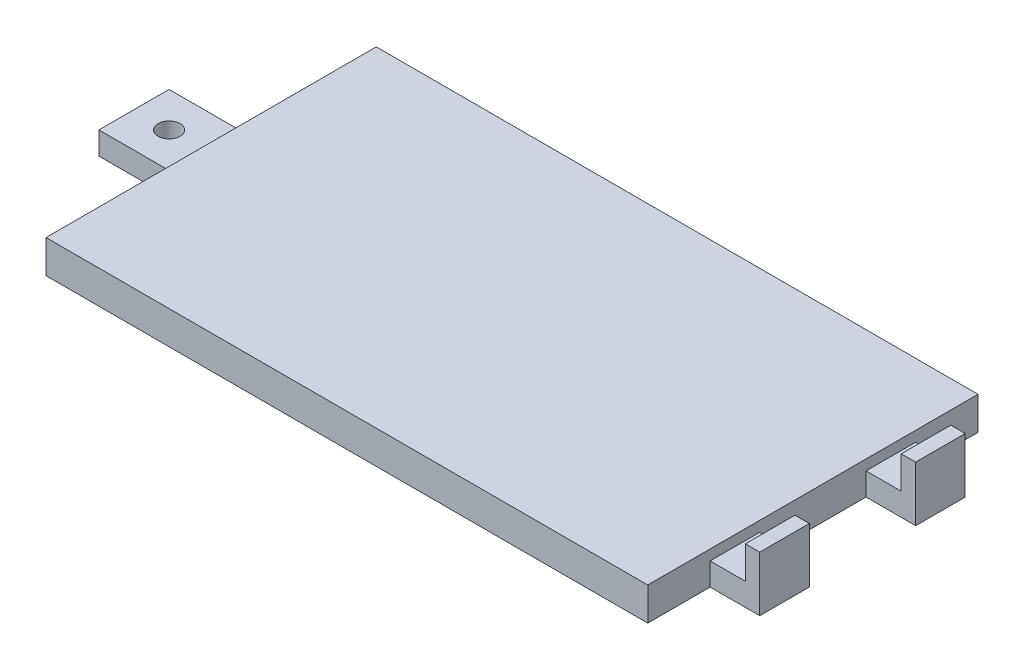
SolidWorks part; units mm, degrees
ref_plane "Front Plane" through (0, 0, 0) normal (0, 0, 1) x (1, 0, 0)
ref_plane "Top Plane" through (0, 0, 0) normal (0, 1, 0) x (1, 0, 0)
ref_plane "Right Plane" through (0, 0, 0) normal (1, 0, 0) x (0, 0, -1)
sketch "Sketch2" plane through (0, 0, 0) normal (0, 1, 0) x (1, 0, 0)
  line L1 (-37.7412, 27.5138) -> (16.8688, 27.5138)
  line L2 (-37.7412, 27.5138) -> (-37.7412, -2.4562)
  line L3 (-37.7412, -2.4562) -> (16.8688, -2.4562)
  line L4 (16.8688, 27.5138) -> (16.8688, -2.4562)
  line L5 (16.8688, 21.8538) -> (21.3688, 21.8538)
  line L6 (16.8688, 21.8538) -> (16.8688, 17.3538)
  line L7 (16.8688, 17.3538) -> (21.3688, 17.3538)
  line L8 (21.3688, 21.8538) -> (21.3688, 17.3538)
  line L9 (16.8688, 7.7038) -> (21.3688, 7.7038)
  line L10 (16.8688, 7.7038) -> (16.8688, 3.2038)
  line L11 (16.8688, 3.2038) -> (21.3688, 3.2038)
  line L12 (21.3688, 7.7038) -> (21.3688, 3.2038)
  line L13 (-37.7412, 15.7138) -> (-44.7412, 15.7138)
  line L14 (-37.7412, 15.7138) -> (-37.7412, 9.3438)
  line L15 (-37.7412, 9.3438) -> (-44.7412, 9.3438)
  line L16 (-44.7412, 15.7138) -> (-44.7412, 9.3438)
  dimension "D1" = 54.61
  dimension "D2" = 29.97
  dimension "D3" = 1.64
  dimension "D4" = 1.64
  dimension "D5" = 7
  dimension "D6" = 5.66
  dimension "D7" = 4.5
  dimension "D8" = 4.5
  dimension "D9" = 4.5
  dimension "D10" = 4.5
  dimension "D11" = 5.66
extrude "Boss-Extrude4" add sketch "Sketch2" along normal blind 3 contours L4 L1 L2 L3 | L13 L16 L15 L2 | L12 L9 L4 L11 | L8 L5 L4 L7
sketch "Sketch3" plane through (0, 3, 0) normal (0, 1, 0) x (1, 0, 0)
  line L1 (-44.7412, 15.7138) -> (-37.7412, 15.7138)
  line L2 (-44.7412, 15.7138) -> (-44.7412, 9.3438)
  line L3 (-44.7412, 9.3438) -> (-37.7412, 9.3438)
  line L4 (-37.7412, 15.7138) -> (-37.7412, 9.3438)
extrude "Boss-Extrude5" add sketch "Sketch3" along normal blind 3
sketch "Sketch4" plane through (0, 3, 0) normal (0, 1, 0) x (1, 0, 0)
  line L0 (21.3688, 7.7038) -> (21.3688, 3.2038) construction
  line L1 (16.8688, 21.8538) -> (21.3688, 21.8538)
  line L2 (16.8688, 21.8538) -> (16.8688, 17.3538)
  line L3 (16.8688, 17.3538) -> (21.3688, 17.3538)
  line L4 (21.3688, 21.8538) -> (21.3688, 17.3538)
  line L5 (16.8688, 7.7038) -> (21.3688, 7.7038)
  line L6 (16.8688, 7.7038) -> (16.8688, 3.2038)
  line L7 (16.8688, 3.2038) -> (21.3688, 3.2038)
  line L8 (21.3688, 7.7038) -> (21.3688, 3.2038)
  line L10 (16.8688, 3.2038) -> (21.3688, 3.2038) construction
extrude "Boss-Extrude6" add sketch "Sketch4" along normal blind 2
sketch "Sketch6" plane through (0, 0, -3.2038) normal (0, 0, 1) x (1, 0, 0)
  line L1 (16.8688, 5) -> (20.0627, 5)
  line L2 (16.8688, 5) -> (16.8688, 2.06)
  line L3 (16.8688, 2.06) -> (20.0627, 2.06)
  line L4 (20.0627, 5) -> (20.0627, 2.06)
  dimension "D1" = 2.94
extrude "Cut-Extrude1" cut sketch "Sketch6" against normal through all both and the other way through all
sketch "Sketch8" plane through (0, 0, -9.3438) normal (0, 0, 1) x (1, 0, 0)
  line L0 (-37.7412, 6) -> (-42.018, 6)
  line L1 (-44.7412, 6) -> (-37.7412, 6) construction
  line L2 (-42.018, 6) -> (-42.018, 6.0125)
  line L3 (-42.018, 6.0125) -> (-43.2476, 6.0125)
  line L4 (-43.2476, 6.0125) -> (-43.2476, 6.0153)
  line L5 (-43.2476, 6.0153) -> (-44.7819, 6.0153)
  line L6 (-44.7819, 6.0153) -> (-44.7819, 2.0586)
  line L7 (-44.7819, 2.0586) -> (-37.7412, 2.0586)
  line L8 (-37.7412, 3) -> (-37.7412, 0) construction
  line L9 (-37.7412, 2.0586) -> (-37.7412, 6)
extrude "Cut-Extrude3" cut sketch "Sketch8" against normal up to next
sketch "Sketch10" plane through (0, 0, 0) normal (0, -1, 0) x (1, 0, 0)
  line L0 (-44.7412, -9.3438) -> (-37.7412, -9.3438) construction
  line L1 (-44.7412, -15.7138) -> (-44.7412, -9.3438) construction
  circle A0 centre (-41.5512, -12.5288) radius 1
  dimension "D1" = 2
  dimension "D2" = 3.185
  dimension "D3" = 3.19
extrude "Cut-Extrude4" cut sketch "Sketch10" against normal blind 5
sketch "Sketch12" plane through (0, 0, 0) normal (0, -1, 0) x (1, 0, 0)
  circle A0 centre (-41.5512, -12.5288) radius 1.25
  dimension "D1" = 2.5
extrude "Cut-Extrude5" cut sketch "Sketch12" against normal blind 0.5
